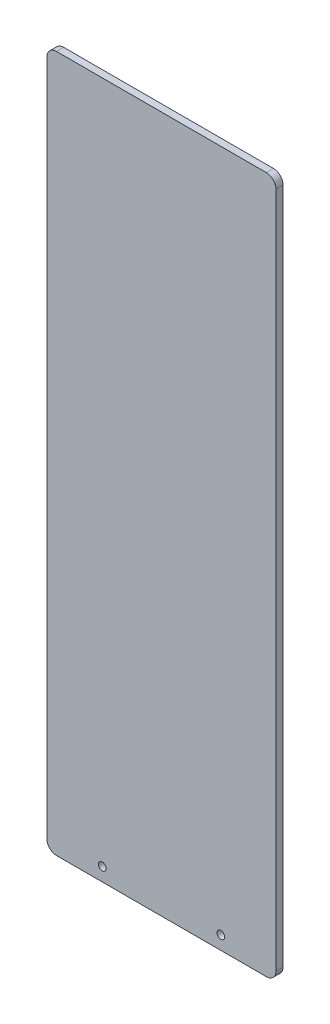
SolidWorks part; units mm, degrees
ref_plane "Front Plane" through (0, 0, 0) normal (0, 0, 1) x (1, 0, 0)
ref_plane "Top Plane" through (0, 0, 0) normal (0, 1, 0) x (1, 0, 0)
ref_plane "Right Plane" through (0, 0, 0) normal (1, 0, 0) x (0, 0, -1)
sketch "Sketch1" plane through (0, 0, 0) normal (0, 0, 1) x (1, 0, 0)
  line L1 (0, 0) -> (152.4, 0)
  line L2 (0, 0) -> (0, 463.55)
  line L3 (0, 463.55) -> (152.4, 463.55)
  line L4 (152.4, 0) -> (152.4, 463.55)
  dimension "D1" = 152.4
  dimension "D2" = 463.55
extrude "Boss-Extrude1" add sketch "Sketch1" along normal blind 4.7625
fillet "Fillet1" radius 6.35 4 edges at (0, 0, 2.3813) (152.4, 0, 2.3813) (0, 463.55, 2.3813) (152.4, 463.55, 2.3813)
sketch "Sketch2" plane through (0, 0, 4.7625) normal (0, 0, 1) x (1, 0, 0)
  circle A0 centre (36.83, 8.9535) radius 2.54
  circle A1 centre (115.7329, 8.9535) radius 2.54
  dimension "D1" = 5.08
extrude "Cut-Extrude1" cut sketch "Sketch2" against normal blind 7.62
